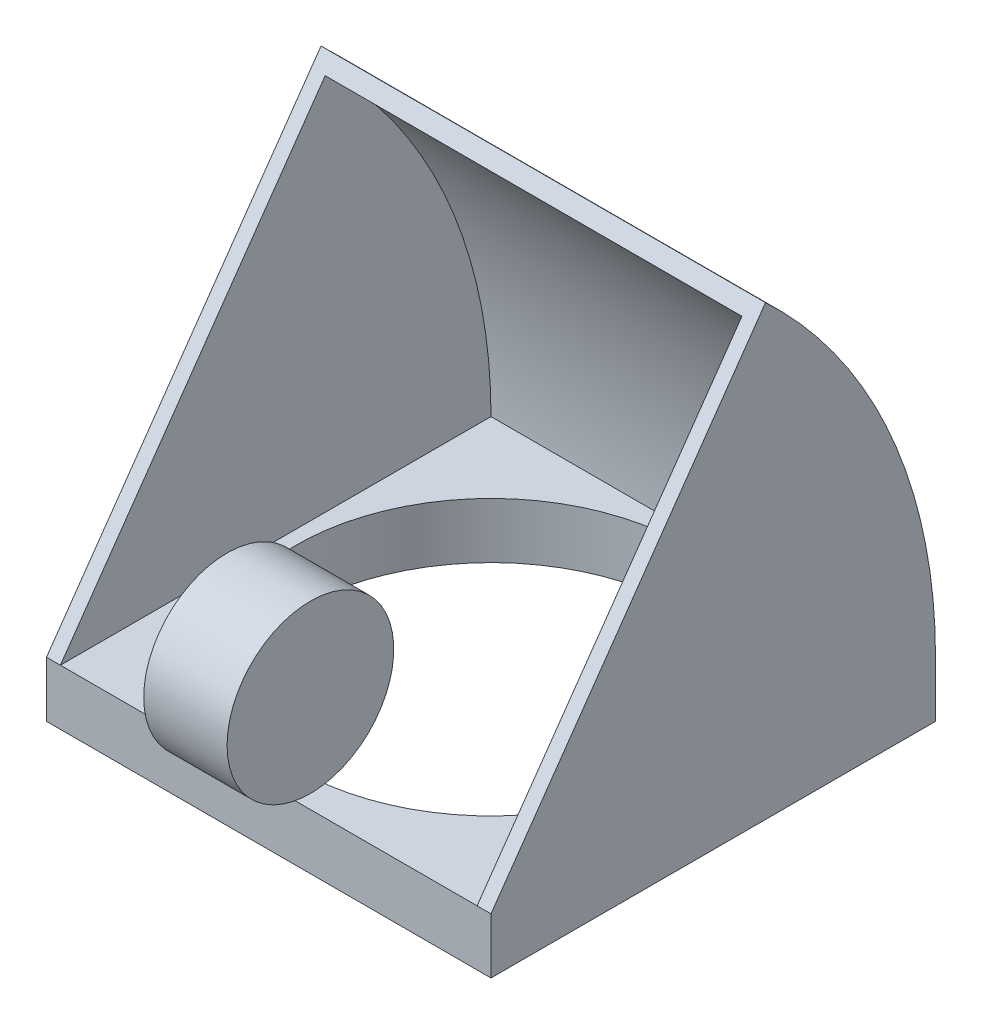
SolidWorks part; units mm, degrees
ref_plane "Front Plane" through (0, 0, 0) normal (0, 0, 1) x (1, 0, 0)
ref_plane "Top Plane" through (0, 0, 0) normal (0, 1, 0) x (1, 0, 0)
ref_plane "Right Plane" through (0, 0, 0) normal (1, 0, 0) x (0, 0, -1)
sketch "Sketch2" plane through (0, 0, 0) normal (0, 1, 0) x (1, 0, 0)
  line L1 (-101.6, 101.6) -> (101.6, 101.6)
  line L2 (-101.6, 101.6) -> (-101.6, -101.6)
  line L3 (-101.6, -101.6) -> (101.6, -101.6)
  line L4 (101.6, 101.6) -> (101.6, -101.6)
  line L5 (-101.6, 101.6) -> (101.6, -101.6) construction
  line L6 (-101.6, -101.6) -> (101.6, 101.6) construction
  circle A0 centre (0, 0) radius 88.9
  point P0 (0, 0)
  dimension "D3" = 177.8
  dimension "D1" = 203.2
  dimension "D2" = 203.2
extrude "Boss-Extrude1" add sketch "Sketch2" along normal blind 25.4
sketch "Sketch3" plane through (101.6, 0, 0) normal (1, 0, 0) x (0, 0, -1)
  line L0 (-101.6, 25.4) -> (23.8932, 204.6229)
  line L1 (101.6, 25.4) -> (-101.6, 25.4)
  line L3 (-101.6, 25.4) -> (101.6, 25.4) construction
  line L4 (101.6, 25.4) -> (101.6, 0) construction
  arc A2 (101.6, 25.4) -> (23.8932, 204.6229) centre (-143.9333, 25.4) ccw
  circle A3 centre (-101.6, 69.85) radius 38.1 construction
  point P5 (0, 0)
  dimension "D1" = 76.2
  dimension "D2" = 146.05
  dimension "D3" = 44.45
  dimension "D4" = 55
extrude "Boss-Extrude2" add sketch "Sketch3" against normal up to surface (203.2 mm away) up to face at (-101.6, 12.7, 0)
sketch "Sketch5" plane through (0, 0, 101.6) normal (0, 0, 1) x (1, 0, 0)
  line L0 (-101.6, 25.4) -> (101.6, 25.4) construction
  line L1 (-95.25, 25.4) -> (95.25, 25.4)
  line L2 (-95.25, 25.4) -> (-95.25, 198.2729)
  line L4 (95.25, 25.4) -> (95.25, 198.2729)
  line L6 (101.6, 204.6229) -> (101.6, 25.4) construction
  line L7 (-101.6, 25.4) -> (-101.6, 204.6229) construction
  line L8 (-95.25, 198.2729) -> (95.25, 198.2729)
  line L9 (-101.6, 204.6229) -> (101.6, 204.6229) construction
  point P6 (95.25, 195.1623)
  point P12 (95.25, 204.6229)
  dimension "D1" = 6.35
  dimension "D2" = 6.35
  dimension "D3" = 6.35
extrude "Cut-Extrude3" cut sketch "Sketch5" against normal offset from surface (196.85 mm away) 6.35
sketch "Sketch6" plane through (0, 0, 0) normal (1, 0, 0) x (0, 0, -1)
  line L2 (23.8932, 204.6229) -> (-101.6, 25.4)
  line L3 (-101.6, 25.4) -> (101.6, 25.4)
  line L4 (23.8932, 204.6229) -> (-101.6, 25.4)
  line L5 (-101.6, 25.4) -> (101.6, 25.4)
  circle A0 centre (-101.6, 69.85) radius 38.1 construction
  arc A1 (101.6, 25.4) -> (23.8932, 204.6229) centre (-143.9333, 25.4) ccw
  arc A2 (101.6, 25.4) -> (23.8932, 204.6229) centre (-143.9333, 25.4) ccw
  circle A3 centre (-101.6, 69.85) radius 38.1
  dimension "D1" = 0
extrude "Boss-Extrude3" add sketch "Sketch6" along normal mid plane 38.1 separate body contours L4 A3 | L4 A3
